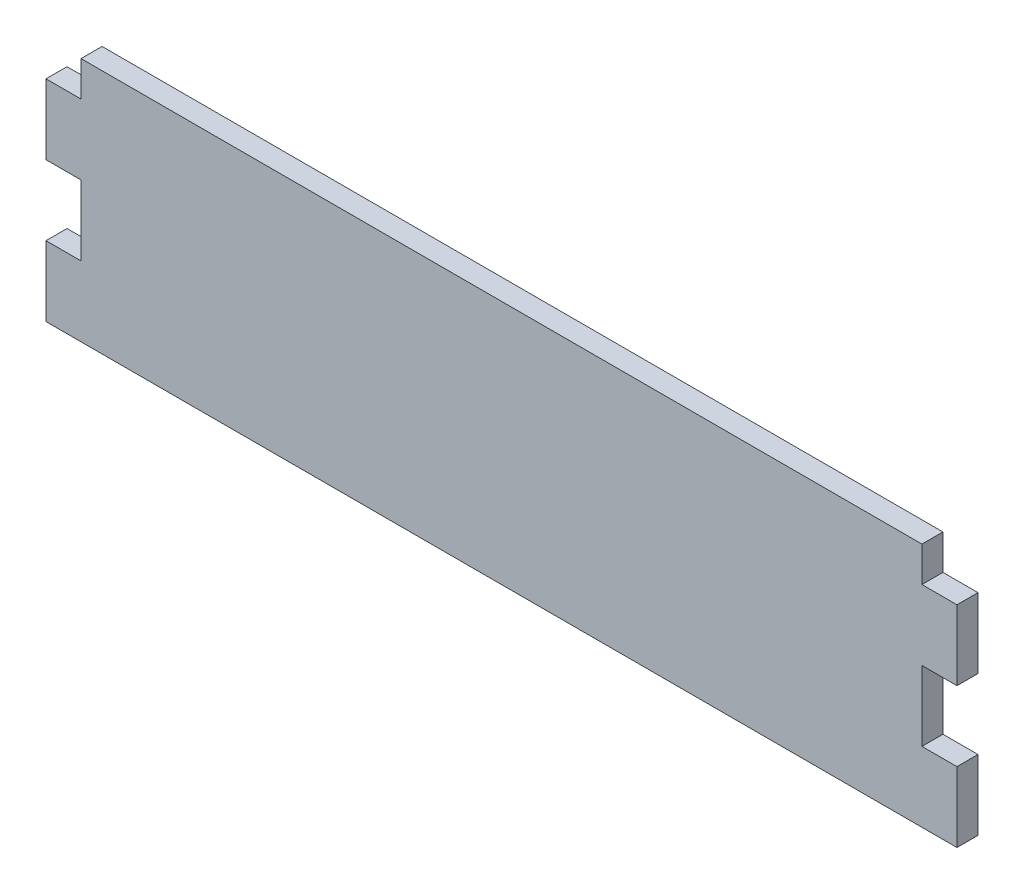
SolidWorks part; units mm, degrees
ref_plane "Plan de face" through (0, 0, 0) normal (0, 0, 1) x (1, 0, 0)
ref_plane "Plan de dessus" through (0, 0, 0) normal (0, 1, 0) x (1, 0, 0)
ref_plane "Plan de droite" through (0, 0, 0) normal (1, 0, 0) x (0, 0, -1)
sketch "Esquisse1" plane through (0, 0, 0) normal (0, 0, 1) x (1, 0, 0)
  line L1 (0, 0) -> (119.98, 0)
  line L2 (0, 0) -> (0, -35)
  line L3 (0, -35) -> (119.98, -35)
  line L4 (119.98, 0) -> (119.98, -35)
  dimension "D1" = 119.98
  dimension "D2" = 35
extrude "Boss.-Extru.1" add sketch "Esquisse1" along normal blind 3
sketch "Esquisse2" plane through (0, 0, 0) normal (-1, 0, 0) x (0, 0, 1)
  line L0 (3, 0) -> (3, -35) construction
  line L1 (0, -35) -> (3, -35)
  line L2 (0, -35) -> (0, -25)
  line L3 (0, -25) -> (3, -25)
  line L4 (3, -35) -> (3, -25)
  dimension "D1" = 10
extrude "Boss.-Extru.2" add sketch "Esquisse2" along normal blind 5
pattern_linear "Répétition linéaire1" count 2 spacing 20 along (0, 1, 0) of "Boss.-Extru.2"
sketch "Esquisse3" plane through (119.98, 0, 0) normal (1, 0, 0) x (0, 0, -1)
  line L0 (0, -35) -> (0, 0) construction
  line L1 (-3, -35) -> (0, -35)
  line L2 (-3, -35) -> (-3, -25)
  line L3 (-3, -25) -> (0, -25)
  line L4 (0, -35) -> (0, -25)
  dimension "D1" = 10
extrude "Boss.-Extru.3" add sketch "Esquisse3" along normal blind 5
pattern_linear "Répétition linéaire2" count 2 spacing 20 along (0, 1, 0) of "Boss.-Extru.3"
